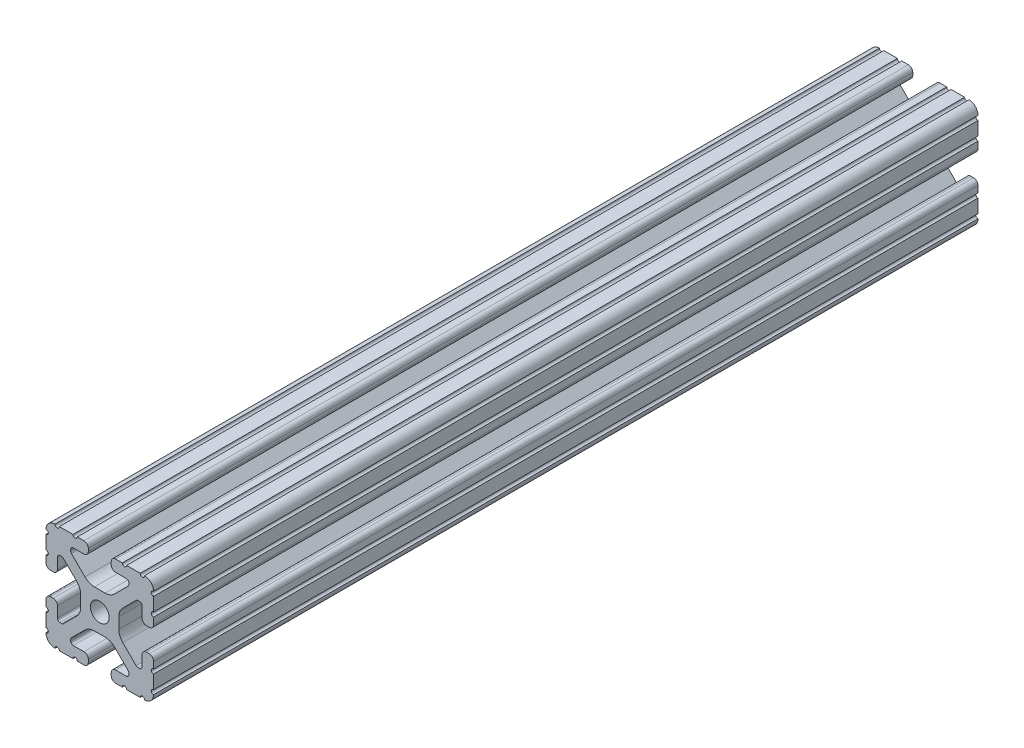
SolidWorks part; units mm, degrees
ref_plane "Front Plane" through (0, 0, 0) normal (0, 0, 1) x (1, 0, 0)
ref_plane "Top Plane" through (0, 0, 0) normal (0, 1, 0) x (1, 0, 0)
ref_plane "Right Plane" through (0, 0, 0) normal (1, 0, 0) x (0, 0, -1)
sketch "Sketch1" plane through (0, 0, 0) normal (0, 0, 1) x (1, 0, 0)
  line L0 (-4.064, 19.05) -> (-4.064, -19.05) construction
  line L1 (-19.05, -19.05) -> (19.05, -19.05) construction
  line L2 (-19.05, -19.05) -> (-19.05, 19.05) construction
  line L3 (-19.05, 19.05) -> (19.05, 19.05) construction
  line L4 (19.05, -19.05) -> (19.05, 19.05) construction
  line L5 (0, 19.05) -> (0, -19.05) construction
  line L6 (-19.05, 0) -> (19.05, 0) construction
  line L7 (-4.064, -19.05) -> (4.064, 19.05) construction
  line L8 (4.064, 19.05) -> (4.064, -19.05) construction
  circle A0 centre (0, 0) radius 3.3274
  point P0 (0, 0)
  line B0 (-10.287, 13.5524) -> (-10.287, 14.0843)
  line B1 (-9.3853, 14.986) -> (-5.6176, 14.986)
  line B2 (-4.064, 16.5396) -> (-4.064, 17.4964)
  line B3 (-5.6176, 19.05) -> (-7.9742, 19.05)
  line B4 (-9.4982, 19.05) -> (-14.3277, 19.05)
  line B5 (-19.05, 14.3277) -> (-19.05, 9.4961)
  line B6 (-19.05, 7.9763) -> (-19.05, 5.6176)
  line B7 (-17.4964, 4.064) -> (-16.5396, 4.064)
  line B8 (-14.986, 5.6176) -> (-14.986, 9.3853)
  line B9 (-14.0843, 10.287) -> (-13.516, 10.287)
  line B10 (-12.8784, 10.0229) -> (-8.1476, 5.2921)
  line B11 (-6.7564, 1.9335) -> (-6.7564, -1.9335)
  line B12 (-8.1476, -5.2921) -> (-12.8784, -10.0229)
  line B13 (-13.516, -10.287) -> (-14.0843, -10.287)
  line B14 (-14.986, -9.3853) -> (-14.986, -5.6176)
  line B15 (-16.5396, -4.064) -> (-17.4964, -4.064)
  line B16 (-19.05, -5.6176) -> (-19.05, -7.9763)
  line B17 (-19.05, -9.4961) -> (-19.05, -14.3277)
  line B18 (-14.3277, -19.05) -> (-9.4961, -19.05)
  line B19 (-7.9763, -19.05) -> (-5.6176, -19.05)
  line B20 (-4.064, -17.4964) -> (-4.064, -16.5396)
  line B21 (-5.6176, -14.986) -> (-9.3853, -14.986)
  line B22 (-10.287, -14.0843) -> (-10.287, -13.5524)
  line B23 (-10.0229, -12.9148) -> (-5.2522, -8.144)
  line B24 (-1.9022, -6.7564) -> (1.9022, -6.7564)
  line B25 (5.2522, -8.144) -> (10.0229, -12.9148)
  line B26 (10.287, -13.5524) -> (10.287, -14.0843)
  line B27 (9.3853, -14.986) -> (5.6176, -14.986)
  line B28 (4.064, -16.5396) -> (4.064, -17.4964)
  line B29 (5.6176, -19.05) -> (7.9763, -19.05)
  line B30 (9.4961, -19.05) -> (14.3277, -19.05)
  line B31 (19.05, -14.3277) -> (19.05, -9.4961)
  line B32 (19.05, -7.9763) -> (19.05, -5.6176)
  line B33 (17.4964, -4.064) -> (16.5396, -4.064)
  line B34 (14.986, -5.6176) -> (14.986, -9.3853)
  line B35 (14.0843, -10.287) -> (13.516, -10.287)
  line B36 (12.8784, -10.0229) -> (8.1476, -5.2921)
  line B37 (6.7564, -1.9335) -> (6.7564, 1.9335)
  line B38 (8.1476, 5.2921) -> (12.8784, 10.0229)
  line B39 (13.516, 10.287) -> (14.0843, 10.287)
  line B40 (14.986, 9.3853) -> (14.986, 5.6176)
  line B41 (16.5396, 4.064) -> (17.4964, 4.064)
  line B42 (19.05, 5.6176) -> (19.05, 7.9763)
  line B43 (19.05, 9.4961) -> (19.05, 14.3277)
  line B44 (14.3277, 19.05) -> (9.4982, 19.05)
  line B45 (7.9742, 19.05) -> (5.6176, 19.05)
  line B46 (4.064, 17.4964) -> (4.064, 16.5396)
  line B47 (5.6176, 14.986) -> (9.3853, 14.986)
  line B48 (10.287, 14.0843) -> (10.287, 13.5524)
  line B49 (10.0229, 12.9148) -> (5.2522, 8.144)
  line B50 (1.9022, 6.7564) -> (-1.9022, 6.7564)
  line B51 (-5.2522, 8.144) -> (-10.0229, 12.9148)
  circle B52 centre (0, 0) radius 3.3274
  arc B53 (-5.6176, 14.986) -> (-4.064, 16.5396) centre (-5.6176, 16.5396) ccw
  arc B54 (-4.064, 17.4964) -> (-5.6176, 19.05) centre (-5.6176, 17.4964) ccw
  arc B55 (-9.4982, 19.05) -> (-7.9742, 19.05) centre (-8.7362, 19.05) ccw
  arc B56 (-15.8475, 19.05) -> (-14.3277, 19.05) centre (-15.0876, 18.9933) ccw
  arc B57 (-15.8475, 19.05) -> (-19.05, 15.8475) centre (-15.8751, 15.8751) ccw
  arc B58 (-19.05, 14.3277) -> (-19.05, 15.8475) centre (-18.9933, 15.0876) ccw
  arc B59 (-19.05, 7.9763) -> (-19.05, 9.4961) centre (-18.9933, 8.7362) ccw
  arc B60 (-19.05, 5.6176) -> (-17.4964, 4.064) centre (-17.4964, 5.6176) ccw
  arc B61 (-16.5396, 4.064) -> (-14.986, 5.6176) centre (-16.5396, 5.6176) ccw
  arc B62 (-14.0843, 10.287) -> (-14.986, 9.3853) centre (-14.0843, 9.3853) ccw
  arc B63 (-12.8784, 10.0229) -> (-13.516, 10.287) centre (-13.516, 9.3853) ccw
  arc B64 (-6.7564, 1.9335) -> (-8.1476, 5.2921) centre (-11.5062, 1.9335) ccw
  arc B65 (-8.1476, -5.2921) -> (-6.7564, -1.9335) centre (-11.5062, -1.9335) ccw
  arc B66 (-13.516, -10.287) -> (-12.8784, -10.0229) centre (-13.516, -9.3853) ccw
  arc B67 (-14.986, -9.3853) -> (-14.0843, -10.287) centre (-14.0843, -9.3853) ccw
  arc B68 (-14.986, -5.6176) -> (-16.5396, -4.064) centre (-16.5396, -5.6176) ccw
  arc B69 (-17.4964, -4.064) -> (-19.05, -5.6176) centre (-17.4964, -5.6176) ccw
  arc B70 (-19.05, -9.4961) -> (-19.05, -7.9763) centre (-18.9933, -8.7362) ccw
  arc B71 (-19.05, -15.8475) -> (-19.05, -14.3277) centre (-18.9933, -15.0876) ccw
  arc B72 (-19.05, -15.8475) -> (-15.8475, -19.05) centre (-15.8751, -15.8751) ccw
  arc B73 (-14.3277, -19.05) -> (-15.8475, -19.05) centre (-15.0876, -18.9933) ccw
  arc B74 (-7.9763, -19.05) -> (-9.4961, -19.05) centre (-8.7362, -18.9933) ccw
  arc B75 (-5.6176, -19.05) -> (-4.064, -17.4964) centre (-5.6176, -17.4964) ccw
  arc B76 (-4.064, -16.5396) -> (-5.6176, -14.986) centre (-5.6176, -16.5396) ccw
  arc B77 (-10.287, -14.0843) -> (-9.3853, -14.986) centre (-9.3853, -14.0843) ccw
  arc B78 (-10.0229, -12.9148) -> (-10.287, -13.5524) centre (-9.3853, -13.5524) ccw
  arc B79 (-1.9022, -6.7564) -> (-5.2522, -8.144) centre (-1.9022, -11.494) ccw
  arc B80 (5.2522, -8.144) -> (1.9022, -6.7564) centre (1.9022, -11.494) ccw
  arc B81 (10.287, -13.5524) -> (10.0229, -12.9148) centre (9.3853, -13.5524) ccw
  arc B82 (9.3853, -14.986) -> (10.287, -14.0843) centre (9.3853, -14.0843) ccw
  arc B83 (5.6176, -14.986) -> (4.064, -16.5396) centre (5.6176, -16.5396) ccw
  arc B84 (4.064, -17.4964) -> (5.6176, -19.05) centre (5.6176, -17.4964) ccw
  arc B85 (9.4961, -19.05) -> (7.9763, -19.05) centre (8.7362, -18.9933) ccw
  arc B86 (15.8475, -19.05) -> (14.3277, -19.05) centre (15.0876, -18.9933) ccw
  arc B87 (15.8475, -19.05) -> (19.05, -15.8475) centre (15.8751, -15.8751) ccw
  arc B88 (19.05, -14.3277) -> (19.05, -15.8475) centre (18.9933, -15.0876) ccw
  arc B89 (19.05, -7.9763) -> (19.05, -9.4961) centre (18.9933, -8.7362) ccw
  arc B90 (19.05, -5.6176) -> (17.4964, -4.064) centre (17.4964, -5.6176) ccw
  arc B91 (16.5396, -4.064) -> (14.986, -5.6176) centre (16.5396, -5.6176) ccw
  arc B92 (14.0843, -10.287) -> (14.986, -9.3853) centre (14.0843, -9.3853) ccw
  arc B93 (12.8784, -10.0229) -> (13.516, -10.287) centre (13.516, -9.3853) ccw
  arc B94 (6.7564, -1.9335) -> (8.1476, -5.2921) centre (11.5062, -1.9335) ccw
  arc B95 (8.1476, 5.2921) -> (6.7564, 1.9335) centre (11.5062, 1.9335) ccw
  arc B96 (13.516, 10.287) -> (12.8784, 10.0229) centre (13.516, 9.3853) ccw
  arc B97 (14.986, 9.3853) -> (14.0843, 10.287) centre (14.0843, 9.3853) ccw
  arc B98 (14.986, 5.6176) -> (16.5396, 4.064) centre (16.5396, 5.6176) ccw
  arc B99 (17.4964, 4.064) -> (19.05, 5.6176) centre (17.4964, 5.6176) ccw
  arc B100 (19.05, 9.4961) -> (19.05, 7.9763) centre (18.9933, 8.7362) ccw
  arc B101 (19.05, 15.8475) -> (19.05, 14.3277) centre (18.9933, 15.0876) ccw
  arc B102 (19.05, 15.8475) -> (15.8475, 19.05) centre (15.8751, 15.8751) ccw
  arc B103 (14.3277, 19.05) -> (15.8475, 19.05) centre (15.0876, 18.9933) ccw
  arc B104 (7.9742, 19.05) -> (9.4982, 19.05) centre (8.7362, 19.05) ccw
  arc B105 (5.6176, 19.05) -> (4.064, 17.4964) centre (5.6176, 17.4964) ccw
  arc B106 (4.064, 16.5396) -> (5.6176, 14.986) centre (5.6176, 16.5396) ccw
  arc B107 (10.287, 14.0843) -> (9.3853, 14.986) centre (9.3853, 14.0843) ccw
  arc B108 (10.0229, 12.9148) -> (10.287, 13.5524) centre (9.3853, 13.5524) ccw
  arc B109 (1.9022, 6.7564) -> (5.2522, 8.144) centre (1.9022, 11.494) ccw
  arc B110 (-5.2522, 8.144) -> (-1.9022, 6.7564) centre (-1.9022, 11.494) ccw
  arc B111 (-10.287, 13.5524) -> (-10.0229, 12.9148) centre (-9.3853, 13.5524) ccw
  dimension "Center Hole Diameter" = 6.6548
  dimension "Rail Width" = 38.1
  dimension "Rail Height" = 38.1
  dimension "T-Slot Width" = 8.128
sketch_block_instance "Block1-1"
sketch_block "Block1"
sketch "Sketch2" plane through (0, 0, 0) normal (1, 0, 0) x (0, 0, -1)
  line L0 (-457.2, 0) -> (457.2, 0) construction
  line L1 (-406.4, 0) -> (-406.4, 19.05) construction
  line L2 (-406.4, 19.05) -> (406.4, 19.05) construction
  line L3 (406.4, 19.05) -> (406.4, 0) construction
  dimension "D1" = 50.8
  dimension "Length" = 914.4
sketch "Sketch3" plane through (0, 0, 0) normal (0, 0, 1) x (1, 0, 0)
  line L0 (-4.064, 16.5396) -> (-4.064, 17.4964) construction
  line L1 (-9.3853, 14.986) -> (-5.6176, 14.986) construction
  line L2 (-10.287, 13.5524) -> (-10.287, 14.0843) construction
  line L3 (-5.2522, 8.144) -> (-10.0229, 12.9148) construction
  line L4 (1.9022, 6.7564) -> (-1.9022, 6.7564) construction
  line L5 (10.0229, 12.9148) -> (5.2522, 8.144) construction
  line L6 (10.287, 14.0843) -> (10.287, 13.5524) construction
  line L7 (5.6176, 14.986) -> (9.3853, 14.986) construction
  line L8 (4.064, 17.4964) -> (4.064, 16.5396) construction
  line L9 (7.9742, 19.05) -> (5.6176, 19.05) construction
  line L10 (14.3277, 19.05) -> (9.4982, 19.05) construction
  line L11 (19.05, 9.4961) -> (19.05, 14.3277) construction
  line L12 (19.05, 5.6176) -> (19.05, 7.9763) construction
  line L13 (16.5396, 4.064) -> (17.4964, 4.064) construction
  line L14 (14.986, 9.3853) -> (14.986, 5.6176) construction
  line L15 (13.516, 10.287) -> (14.0843, 10.287) construction
  line L16 (8.1476, 5.2921) -> (12.8784, 10.0229) construction
  line L17 (6.7564, -1.9335) -> (6.7564, 1.9335) construction
  line L18 (12.8784, -10.0229) -> (8.1476, -5.2921) construction
  line L19 (14.0843, -10.287) -> (13.516, -10.287) construction
  line L20 (14.986, -5.6176) -> (14.986, -9.3853) construction
  line L21 (17.4964, -4.064) -> (16.5396, -4.064) construction
  line L22 (19.05, -7.9763) -> (19.05, -5.6176) construction
  line L23 (19.05, -14.3277) -> (19.05, -9.4961) construction
  line L24 (9.4961, -19.05) -> (14.3277, -19.05) construction
  line L25 (5.6176, -19.05) -> (7.9763, -19.05) construction
  line L26 (4.064, -16.5396) -> (4.064, -17.4964) construction
  line L27 (9.3853, -14.986) -> (5.6176, -14.986) construction
  line L28 (10.287, -13.5524) -> (10.287, -14.0843) construction
  line L29 (5.2522, -8.144) -> (10.0229, -12.9148) construction
  line L30 (-1.9022, -6.7564) -> (1.9022, -6.7564) construction
  line L31 (-10.0229, -12.9148) -> (-5.2522, -8.144) construction
  line L32 (-10.287, -14.0843) -> (-10.287, -13.5524) construction
  line L33 (-5.6176, -14.986) -> (-9.3853, -14.986) construction
  line L34 (-4.064, -17.4964) -> (-4.064, -16.5396) construction
  line L35 (-7.9763, -19.05) -> (-5.6176, -19.05) construction
  line L36 (-14.3277, -19.05) -> (-9.4961, -19.05) construction
  line L37 (-19.05, -9.4961) -> (-19.05, -14.3277) construction
  line L38 (-19.05, -5.6176) -> (-19.05, -7.9763) construction
  line L39 (-16.5396, -4.064) -> (-17.4964, -4.064) construction
  line L40 (-14.986, -9.3853) -> (-14.986, -5.6176) construction
  line L41 (-13.516, -10.287) -> (-14.0843, -10.287) construction
  line L42 (-8.1476, -5.2921) -> (-12.8784, -10.0229) construction
  line L43 (-6.7564, 1.9335) -> (-6.7564, -1.9335) construction
  line L44 (-12.8784, 10.0229) -> (-8.1476, 5.2921) construction
  line L45 (-14.0843, 10.287) -> (-13.516, 10.287) construction
  line L46 (-14.986, 5.6176) -> (-14.986, 9.3853) construction
  line L47 (-17.4964, 4.064) -> (-16.5396, 4.064) construction
  line L48 (-19.05, 7.9763) -> (-19.05, 5.6176) construction
  line L49 (-19.05, 14.3277) -> (-19.05, 9.4961) construction
  line L50 (-9.4982, 19.05) -> (-14.3277, 19.05) construction
  line L51 (-5.6176, 19.05) -> (-7.9742, 19.05) construction
  line L52 (-4.064, 16.5396) -> (-4.064, 17.4964)
  line L53 (-9.3853, 14.986) -> (-5.6176, 14.986)
  line L54 (-10.287, 13.5524) -> (-10.287, 14.0843)
  line L55 (-5.2522, 8.144) -> (-10.0229, 12.9148)
  line L56 (1.9022, 6.7564) -> (-1.9022, 6.7564)
  line L57 (10.0229, 12.9148) -> (5.2522, 8.144)
  line L58 (10.287, 14.0843) -> (10.287, 13.5524)
  line L59 (5.6176, 14.986) -> (9.3853, 14.986)
  line L60 (4.064, 17.4964) -> (4.064, 16.5396)
  line L61 (7.9742, 19.05) -> (5.6176, 19.05)
  line L62 (14.3277, 19.05) -> (9.4982, 19.05)
  line L63 (19.05, 9.4961) -> (19.05, 14.3277)
  line L64 (19.05, 5.6176) -> (19.05, 7.9763)
  line L65 (16.5396, 4.064) -> (17.4964, 4.064)
  line L66 (14.986, 9.3853) -> (14.986, 5.6176)
  line L67 (13.516, 10.287) -> (14.0843, 10.287)
  line L68 (8.1476, 5.2921) -> (12.8784, 10.0229)
  line L69 (6.7564, -1.9335) -> (6.7564, 1.9335)
  line L70 (12.8784, -10.0229) -> (8.1476, -5.2921)
  line L71 (14.0843, -10.287) -> (13.516, -10.287)
  line L72 (14.986, -5.6176) -> (14.986, -9.3853)
  line L73 (17.4964, -4.064) -> (16.5396, -4.064)
  line L74 (19.05, -7.9763) -> (19.05, -5.6176)
  line L75 (19.05, -14.3277) -> (19.05, -9.4961)
  line L76 (9.4961, -19.05) -> (14.3277, -19.05)
  line L77 (5.6176, -19.05) -> (7.9763, -19.05)
  line L78 (4.064, -16.5396) -> (4.064, -17.4964)
  line L79 (9.3853, -14.986) -> (5.6176, -14.986)
  line L80 (10.287, -13.5524) -> (10.287, -14.0843)
  line L81 (5.2522, -8.144) -> (10.0229, -12.9148)
  line L82 (-1.9022, -6.7564) -> (1.9022, -6.7564)
  line L83 (-10.0229, -12.9148) -> (-5.2522, -8.144)
  line L84 (-10.287, -14.0843) -> (-10.287, -13.5524)
  line L85 (-5.6176, -14.986) -> (-9.3853, -14.986)
  line L86 (-4.064, -17.4964) -> (-4.064, -16.5396)
  line L87 (-7.9763, -19.05) -> (-5.6176, -19.05)
  line L88 (-14.3277, -19.05) -> (-9.4961, -19.05)
  line L89 (-19.05, -9.4961) -> (-19.05, -14.3277)
  line L90 (-19.05, -5.6176) -> (-19.05, -7.9763)
  line L91 (-16.5396, -4.064) -> (-17.4964, -4.064)
  line L92 (-14.986, -9.3853) -> (-14.986, -5.6176)
  line L93 (-13.516, -10.287) -> (-14.0843, -10.287)
  line L94 (-8.1476, -5.2921) -> (-12.8784, -10.0229)
  line L95 (-6.7564, 1.9335) -> (-6.7564, -1.9335)
  line L96 (-12.8784, 10.0229) -> (-8.1476, 5.2921)
  line L97 (-14.0843, 10.287) -> (-13.516, 10.287)
  line L98 (-14.986, 5.6176) -> (-14.986, 9.3853)
  line L99 (-17.4964, 4.064) -> (-16.5396, 4.064)
  line L100 (-19.05, 7.9763) -> (-19.05, 5.6176)
  line L101 (-19.05, 14.3277) -> (-19.05, 9.4961)
  line L102 (-9.4982, 19.05) -> (-14.3277, 19.05)
  line L103 (-5.6176, 19.05) -> (-7.9742, 19.05)
  circle A0 centre (0, 0) radius 3.3274 construction
  circle A1 centre (0, 0) radius 3.3274
  circle A2 centre (0, 0) radius 3.3274
  arc A3 (-5.6176, 14.986) -> (-4.064, 16.5396) centre (-5.6176, 16.5396) ccw construction
  arc A4 (-9.3853, 14.986) -> (-10.287, 14.0843) centre (-9.3853, 14.0843) ccw construction
  arc A5 (-10.287, 13.5524) -> (-10.0229, 12.9148) centre (-9.3853, 13.5524) ccw construction
  arc A6 (-5.2522, 8.144) -> (-1.9022, 6.7564) centre (-1.9022, 11.494) ccw construction
  arc A7 (1.9022, 6.7564) -> (5.2522, 8.144) centre (1.9022, 11.494) ccw construction
  arc A8 (10.0229, 12.9148) -> (10.287, 13.5524) centre (9.3853, 13.5524) ccw construction
  arc A9 (10.287, 14.0843) -> (9.3853, 14.986) centre (9.3853, 14.0843) ccw construction
  arc A10 (4.064, 16.5396) -> (5.6176, 14.986) centre (5.6176, 16.5396) ccw construction
  arc A11 (5.6176, 19.05) -> (4.064, 17.4964) centre (5.6176, 17.4964) ccw construction
  arc A12 (7.9742, 19.05) -> (9.4982, 19.05) centre (8.7362, 19.05) ccw construction
  arc A13 (14.3277, 19.05) -> (15.8475, 19.05) centre (15.0876, 18.9933) ccw construction
  arc A14 (19.05, 15.8475) -> (15.8475, 19.05) centre (15.8751, 15.8751) ccw construction
  arc A15 (19.05, 15.8475) -> (19.05, 14.3277) centre (18.9933, 15.0876) ccw construction
  arc A16 (19.05, 9.4961) -> (19.05, 7.9763) centre (18.9933, 8.7362) ccw construction
  arc A17 (17.4964, 4.064) -> (19.05, 5.6176) centre (17.4964, 5.6176) ccw construction
  arc A18 (14.986, 5.6176) -> (16.5396, 4.064) centre (16.5396, 5.6176) ccw construction
  arc A19 (14.986, 9.3853) -> (14.0843, 10.287) centre (14.0843, 9.3853) ccw construction
  arc A20 (13.516, 10.287) -> (12.8784, 10.0229) centre (13.516, 9.3853) ccw construction
  arc A21 (8.1476, 5.2921) -> (6.7564, 1.9335) centre (11.5062, 1.9335) ccw construction
  arc A22 (6.7564, -1.9335) -> (8.1476, -5.2921) centre (11.5062, -1.9335) ccw construction
  arc A23 (12.8784, -10.0229) -> (13.516, -10.287) centre (13.516, -9.3853) ccw construction
  arc A24 (14.0843, -10.287) -> (14.986, -9.3853) centre (14.0843, -9.3853) ccw construction
  arc A25 (16.5396, -4.064) -> (14.986, -5.6176) centre (16.5396, -5.6176) ccw construction
  arc A26 (19.05, -5.6176) -> (17.4964, -4.064) centre (17.4964, -5.6176) ccw construction
  arc A27 (19.05, -7.9763) -> (19.05, -9.4961) centre (18.9933, -8.7362) ccw construction
  arc A28 (19.05, -14.3277) -> (19.05, -15.8475) centre (18.9933, -15.0876) ccw construction
  arc A29 (15.8475, -19.05) -> (19.05, -15.8475) centre (15.8751, -15.8751) ccw construction
  arc A30 (15.8475, -19.05) -> (14.3277, -19.05) centre (15.0876, -18.9933) ccw construction
  arc A31 (9.4961, -19.05) -> (7.9763, -19.05) centre (8.7362, -18.9933) ccw construction
  arc A32 (4.064, -17.4964) -> (5.6176, -19.05) centre (5.6176, -17.4964) ccw construction
  arc A33 (5.6176, -14.986) -> (4.064, -16.5396) centre (5.6176, -16.5396) ccw construction
  arc A34 (9.3853, -14.986) -> (10.287, -14.0843) centre (9.3853, -14.0843) ccw construction
  arc A35 (10.287, -13.5524) -> (10.0229, -12.9148) centre (9.3853, -13.5524) ccw construction
  arc A36 (5.2522, -8.144) -> (1.9022, -6.7564) centre (1.9022, -11.494) ccw construction
  arc A37 (-1.9022, -6.7564) -> (-5.2522, -8.144) centre (-1.9022, -11.494) ccw construction
  arc A38 (-10.0229, -12.9148) -> (-10.287, -13.5524) centre (-9.3853, -13.5524) ccw construction
  arc A39 (-10.287, -14.0843) -> (-9.3853, -14.986) centre (-9.3853, -14.0843) ccw construction
  arc A40 (-4.064, -16.5396) -> (-5.6176, -14.986) centre (-5.6176, -16.5396) ccw construction
  arc A41 (-5.6176, -19.05) -> (-4.064, -17.4964) centre (-5.6176, -17.4964) ccw construction
  arc A42 (-7.9763, -19.05) -> (-9.4961, -19.05) centre (-8.7362, -18.9933) ccw construction
  arc A43 (-14.3277, -19.05) -> (-15.8475, -19.05) centre (-15.0876, -18.9933) ccw construction
  arc A44 (-19.05, -15.8475) -> (-15.8475, -19.05) centre (-15.8751, -15.8751) ccw construction
  arc A45 (-19.05, -15.8475) -> (-19.05, -14.3277) centre (-18.9933, -15.0876) ccw construction
  arc A46 (-19.05, -9.4961) -> (-19.05, -7.9763) centre (-18.9933, -8.7362) ccw construction
  arc A47 (-17.4964, -4.064) -> (-19.05, -5.6176) centre (-17.4964, -5.6176) ccw construction
  arc A48 (-14.986, -5.6176) -> (-16.5396, -4.064) centre (-16.5396, -5.6176) ccw construction
  arc A49 (-14.986, -9.3853) -> (-14.0843, -10.287) centre (-14.0843, -9.3853) ccw construction
  arc A50 (-13.516, -10.287) -> (-12.8784, -10.0229) centre (-13.516, -9.3853) ccw construction
  arc A51 (-8.1476, -5.2921) -> (-6.7564, -1.9335) centre (-11.5062, -1.9335) ccw construction
  arc A52 (-6.7564, 1.9335) -> (-8.1476, 5.2921) centre (-11.5062, 1.9335) ccw construction
  arc A53 (-12.8784, 10.0229) -> (-13.516, 10.287) centre (-13.516, 9.3853) ccw construction
  arc A54 (-14.0843, 10.287) -> (-14.986, 9.3853) centre (-14.0843, 9.3853) ccw construction
  arc A55 (-16.5396, 4.064) -> (-14.986, 5.6176) centre (-16.5396, 5.6176) ccw construction
  arc A56 (-19.05, 5.6176) -> (-17.4964, 4.064) centre (-17.4964, 5.6176) ccw construction
  arc A57 (-19.05, 7.9763) -> (-19.05, 9.4961) centre (-18.9933, 8.7362) ccw construction
  arc A58 (-19.05, 14.3277) -> (-19.05, 15.8475) centre (-18.9933, 15.0876) ccw construction
  arc A59 (-15.8475, 19.05) -> (-19.05, 15.8475) centre (-15.8751, 15.8751) ccw construction
  arc A60 (-15.8475, 19.05) -> (-14.3277, 19.05) centre (-15.0876, 18.9933) ccw construction
  arc A61 (-9.4982, 19.05) -> (-7.9742, 19.05) centre (-8.7362, 19.05) ccw construction
  arc A62 (-4.064, 17.4964) -> (-5.6176, 19.05) centre (-5.6176, 17.4964) ccw construction
  circle A63 centre (0, 0) radius 3.3274
  arc A64 (-5.6176, 14.986) -> (-4.064, 16.5396) centre (-5.6176, 16.5396) ccw
  arc A65 (-9.3853, 14.986) -> (-10.287, 14.0843) centre (-9.3853, 14.0843) ccw
  arc A66 (-10.287, 13.5524) -> (-10.0229, 12.9148) centre (-9.3853, 13.5524) ccw
  arc A67 (-5.2522, 8.144) -> (-1.9022, 6.7564) centre (-1.9022, 11.494) ccw
  arc A68 (1.9022, 6.7564) -> (5.2522, 8.144) centre (1.9022, 11.494) ccw
  arc A69 (10.0229, 12.9148) -> (10.287, 13.5524) centre (9.3853, 13.5524) ccw
  arc A70 (10.287, 14.0843) -> (9.3853, 14.986) centre (9.3853, 14.0843) ccw
  arc A71 (4.064, 16.5396) -> (5.6176, 14.986) centre (5.6176, 16.5396) ccw
  arc A72 (5.6176, 19.05) -> (4.064, 17.4964) centre (5.6176, 17.4964) ccw
  arc A73 (7.9742, 19.05) -> (9.4982, 19.05) centre (8.7362, 19.05) ccw
  arc A74 (14.3277, 19.05) -> (15.8475, 19.05) centre (15.0876, 18.9933) ccw
  arc A75 (19.05, 15.8475) -> (15.8475, 19.05) centre (15.8751, 15.8751) ccw
  arc A76 (19.05, 15.8475) -> (19.05, 14.3277) centre (18.9933, 15.0876) ccw
  arc A77 (19.05, 9.4961) -> (19.05, 7.9763) centre (18.9933, 8.7362) ccw
  arc A78 (17.4964, 4.064) -> (19.05, 5.6176) centre (17.4964, 5.6176) ccw
  arc A79 (14.986, 5.6176) -> (16.5396, 4.064) centre (16.5396, 5.6176) ccw
  arc A80 (14.986, 9.3853) -> (14.0843, 10.287) centre (14.0843, 9.3853) ccw
  arc A81 (13.516, 10.287) -> (12.8784, 10.0229) centre (13.516, 9.3853) ccw
  arc A82 (8.1476, 5.2921) -> (6.7564, 1.9335) centre (11.5062, 1.9335) ccw
  arc A83 (6.7564, -1.9335) -> (8.1476, -5.2921) centre (11.5062, -1.9335) ccw
  arc A84 (12.8784, -10.0229) -> (13.516, -10.287) centre (13.516, -9.3853) ccw
  arc A85 (14.0843, -10.287) -> (14.986, -9.3853) centre (14.0843, -9.3853) ccw
  arc A86 (16.5396, -4.064) -> (14.986, -5.6176) centre (16.5396, -5.6176) ccw
  arc A87 (19.05, -5.6176) -> (17.4964, -4.064) centre (17.4964, -5.6176) ccw
  arc A88 (19.05, -7.9763) -> (19.05, -9.4961) centre (18.9933, -8.7362) ccw
  arc A89 (19.05, -14.3277) -> (19.05, -15.8475) centre (18.9933, -15.0876) ccw
  arc A90 (15.8475, -19.05) -> (19.05, -15.8475) centre (15.8751, -15.8751) ccw
  arc A91 (15.8475, -19.05) -> (14.3277, -19.05) centre (15.0876, -18.9933) ccw
  arc A92 (9.4961, -19.05) -> (7.9763, -19.05) centre (8.7362, -18.9933) ccw
  arc A93 (4.064, -17.4964) -> (5.6176, -19.05) centre (5.6176, -17.4964) ccw
  arc A94 (5.6176, -14.986) -> (4.064, -16.5396) centre (5.6176, -16.5396) ccw
  arc A95 (9.3853, -14.986) -> (10.287, -14.0843) centre (9.3853, -14.0843) ccw
  arc A96 (10.287, -13.5524) -> (10.0229, -12.9148) centre (9.3853, -13.5524) ccw
  arc A97 (5.2522, -8.144) -> (1.9022, -6.7564) centre (1.9022, -11.494) ccw
  arc A98 (-1.9022, -6.7564) -> (-5.2522, -8.144) centre (-1.9022, -11.494) ccw
  arc A99 (-10.0229, -12.9148) -> (-10.287, -13.5524) centre (-9.3853, -13.5524) ccw
  arc A100 (-10.287, -14.0843) -> (-9.3853, -14.986) centre (-9.3853, -14.0843) ccw
  arc A101 (-4.064, -16.5396) -> (-5.6176, -14.986) centre (-5.6176, -16.5396) ccw
  arc A102 (-5.6176, -19.05) -> (-4.064, -17.4964) centre (-5.6176, -17.4964) ccw
  arc A103 (-7.9763, -19.05) -> (-9.4961, -19.05) centre (-8.7362, -18.9933) ccw
  arc A104 (-14.3277, -19.05) -> (-15.8475, -19.05) centre (-15.0876, -18.9933) ccw
  arc A105 (-19.05, -15.8475) -> (-15.8475, -19.05) centre (-15.8751, -15.8751) ccw
  arc A106 (-19.05, -15.8475) -> (-19.05, -14.3277) centre (-18.9933, -15.0876) ccw
  arc A107 (-19.05, -9.4961) -> (-19.05, -7.9763) centre (-18.9933, -8.7362) ccw
  arc A108 (-17.4964, -4.064) -> (-19.05, -5.6176) centre (-17.4964, -5.6176) ccw
  arc A109 (-14.986, -5.6176) -> (-16.5396, -4.064) centre (-16.5396, -5.6176) ccw
  arc A110 (-14.986, -9.3853) -> (-14.0843, -10.287) centre (-14.0843, -9.3853) ccw
  arc A111 (-13.516, -10.287) -> (-12.8784, -10.0229) centre (-13.516, -9.3853) ccw
  arc A112 (-8.1476, -5.2921) -> (-6.7564, -1.9335) centre (-11.5062, -1.9335) ccw
  arc A113 (-6.7564, 1.9335) -> (-8.1476, 5.2921) centre (-11.5062, 1.9335) ccw
  arc A114 (-12.8784, 10.0229) -> (-13.516, 10.287) centre (-13.516, 9.3853) ccw
  arc A115 (-14.0843, 10.287) -> (-14.986, 9.3853) centre (-14.0843, 9.3853) ccw
  arc A116 (-16.5396, 4.064) -> (-14.986, 5.6176) centre (-16.5396, 5.6176) ccw
  arc A117 (-19.05, 5.6176) -> (-17.4964, 4.064) centre (-17.4964, 5.6176) ccw
  arc A118 (-19.05, 7.9763) -> (-19.05, 9.4961) centre (-18.9933, 8.7362) ccw
  arc A119 (-19.05, 14.3277) -> (-19.05, 15.8475) centre (-18.9933, 15.0876) ccw
  arc A120 (-15.8475, 19.05) -> (-19.05, 15.8475) centre (-15.8751, 15.8751) ccw
  arc A121 (-15.8475, 19.05) -> (-14.3277, 19.05) centre (-15.0876, 18.9933) ccw
  arc A122 (-9.4982, 19.05) -> (-7.9742, 19.05) centre (-8.7362, 19.05) ccw
  arc A123 (-4.064, 17.4964) -> (-5.6176, 19.05) centre (-5.6176, 17.4964) ccw
  dimension "D1" = 0
extrude "Boss-Extrude1" add sketch "Sketch3" along normal up to vertex (457.2 mm away) and the other way up to vertex (457.2 mm away) contours L52 A123 L103 A122 L102 A121 A120 A119 L101 A118 L100 A117 L99 A116 L98 A115 L97 A114 L96 A113 L95 A112 L94 A111 L93 A110 L92 A109 L91 A108 L90 A107 L89 A106 A105 A104 L88 A103 L87 A102 L86 A101 L85 A100 L84 A99 L83 A98 L82 A97 L81 up to point (0, 0, 457.2) other way up to point (0, 0, -457.2)
sketch "Sketch4" plane through (0, 0, 0) normal (0, 1, 0) x (1, 0, 0)
  line L0 (-11.9129, 457.2) -> (-11.9129, 165.1) construction
  line L1 (-9.4982, 457.2) -> (-14.3277, 457.2) construction
  line L9 (-11.9129, 165.1) -> (-26.026, 165.1)
  line L10 (-26.026, 165.1) -> (-26.026, -481.323)
  line L11 (-26.026, -481.323) -> (32.6353, -481.323)
  line L12 (32.6353, -481.323) -> (32.6353, 165.1)
  line L13 (32.6353, 165.1) -> (-11.9129, 165.1)
extrude "Cut-Extrude1" cut sketch "Sketch4" against normal mid plane 45.72
